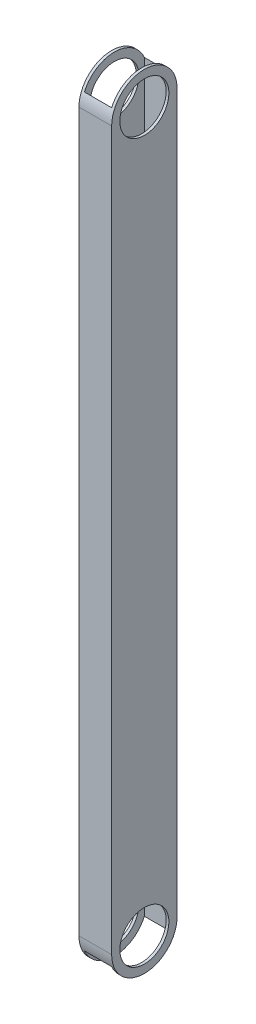
SolidWorks part; units mm, degrees
ref_plane "Front Plane" through (0, 0, 0) normal (0, 0, 1) x (1, 0, 0)
ref_plane "Top Plane" through (0, 0, 0) normal (0, 1, 0) x (1, 0, 0)
ref_plane "Right Plane" through (0, 0, 0) normal (1, 0, 0) x (0, 0, -1)
sketch "Sketch2" plane through (0, 0, 0) normal (0, 1, 0) x (1, 0, 0)
  line L1 (0, 0) -> (19.05, 0)
  line L2 (0, 0) -> (0, 38.1)
  line L3 (0, 38.1) -> (19.05, 38.1)
  line L4 (19.05, 0) -> (19.05, 38.1)
  dimension "D1" = 38.1
  dimension "D2" = 19.05
extrude "Extrude-Thin1" add sketch "Sketch2" along normal blind 456.184 thin thin type one direction reverse wall 1.5875
sketch "Sketch3" plane through (0, 0, 0) normal (-1, 0, 0) x (0, 0, 1)
  line L3 (-38.1, 19.05) -> (-38.1, 0)
  line L4 (-38.1, 0) -> (0, 0)
  line L5 (0, 0) -> (0, 19.05)
  line L6 (-38.1, 437.134) -> (-38.1, 456.184)
  line L7 (-38.1, 456.184) -> (-38.1, 0) construction
  line L8 (-38.1, 456.184) -> (0, 456.184) construction
  line L9 (-38.1, 456.184) -> (0, 456.184)
  line L10 (0, 456.184) -> (0, 437.134)
  circle A0 centre (-19.05, 19.05) radius 14.2875
  circle A1 centre (-19.05, 437.134) radius 14.2875
  arc A2 (-38.1, 19.05) -> (0, 19.05) centre (-19.05, 19.05) ccw
  arc A3 (0, 437.134) -> (-38.1, 437.134) centre (-19.05, 437.134) ccw
  line M1 (-38.1, 0) -> (0, 0)
  line M2 (0, 0) -> (0, 456.184)
  line M3 (0, 456.184) -> (-38.1, 456.184)
  line M4 (-38.1, 456.184) -> (-38.1, 0)
  dimension "D1" = 28.575
  dimension "D3" = 28.575
extrude "Cut-Extrude1" cut sketch "Sketch3" against normal through all contours A0 | A2 M4 M1 | A2 L4 M2 | A1 | A3 L9 M4 | A3 M2 M3
